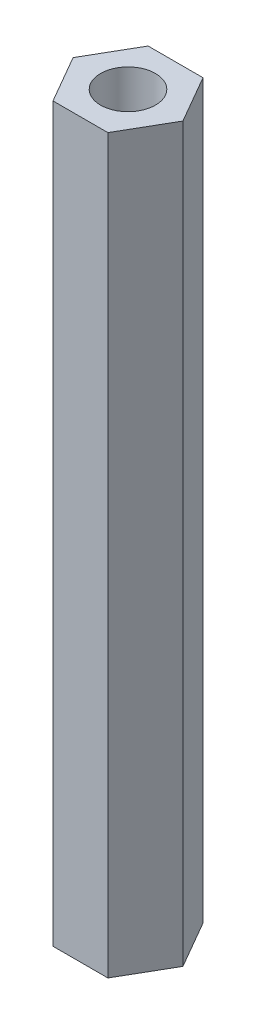
SolidWorks part; units mm, degrees
ref_plane "前视基准面" through (0, 0, 0) normal (0, 0, 1) x (1, 0, 0)
ref_plane "上视基准面" through (0, 0, 0) normal (0, 1, 0) x (1, 0, 0)
ref_plane "右视基准面" through (0, 0, 0) normal (1, 0, 0) x (0, 0, -1)
sketch "草图1" plane through (0, 0, 0) normal (0, 1, 0) x (1, 0, 0)
  line L7 (3, 0) -> (1.5, 2.5981)
  line L8 (1.5, 2.5981) -> (-1.5, 2.5981)
  line L9 (-1.5, 2.5981) -> (-3, 0)
  line L10 (-3, 0) -> (-1.5, -2.5981)
  line L11 (-1.5, -2.5981) -> (1.5, -2.5981)
  line L12 (1.5, -2.5981) -> (3, 0)
  circle A2 centre (0, 0) radius 2.5981 construction
  circle A3 centre (0, 0) radius 1.5
  dimension "D2" = 3
  dimension "D3" = 3
extrude "凸台-拉伸1" add sketch "草图1" along normal blind 40
